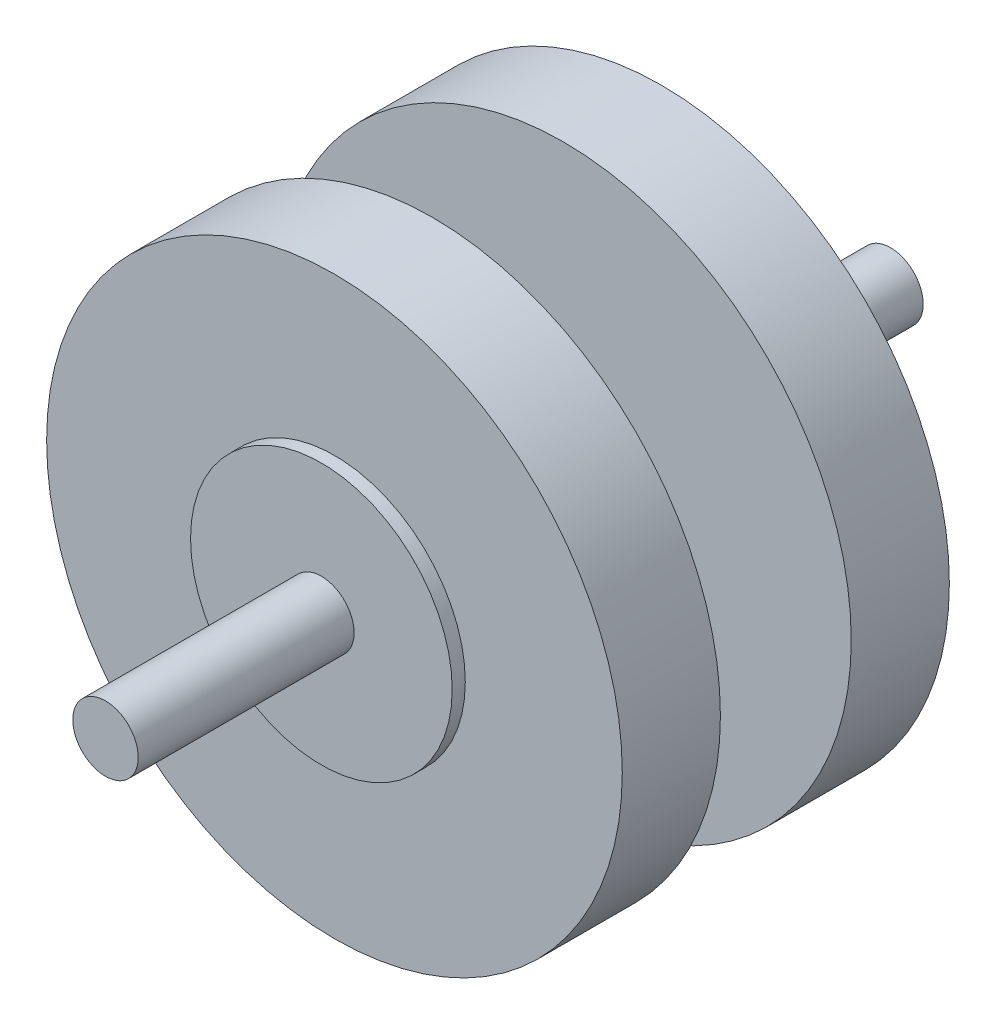
SolidWorks part; units mm, degrees
ref_plane "Płaszczyzna przednia" through (0, 0, 0) normal (0, 0, 1) x (1, 0, 0)
ref_plane "Płaszczyzna górna" through (0, 0, 0) normal (0, 1, 0) x (1, 0, 0)
ref_plane "Płaszczyzna prawa" through (0, 0, 0) normal (1, 0, 0) x (0, 0, -1)
sketch "Szkic1" plane through (0, 0, 0) normal (0, 0, 1) x (1, 0, 0)
  line L0 (0, 5) -> (0, -5) construction
  arc A0 (0, -5) -> (0, 5) centre (0, 0) ccw construction
  circle A1 centre (0, 0) radius 5
extrude "Dodanie-wyciągnięcie1" add sketch "Szkic1" against normal blind 33
sketch "Szkic2" plane through (0, 0, -33) normal (0, 0, -1) x (-1, 0, 0)
  circle A0 centre (0, 0) radius 20
  dimension "D1" = 40
extrude "Dodanie-wyciągnięcie2" add sketch "Szkic2" along normal blind 2
sketch "Szkic3" plane through (0, 0, -35) normal (0, 0, -1) x (-1, 0, 0)
  circle A0 centre (0, 0) radius 44
  dimension "D1" = 88
extrude "Dodanie-wyciągnięcie3" add sketch "Szkic3" along normal blind 15
sketch "Szkic5" plane through (0, 0, -50) normal (0, 0, -1) x (-1, 0, 0)
  circle A0 centre (9.135, -17.7919) radius 5 construction
  circle A1 centre (9.135, -17.7919) radius 5
extrude "Dodanie-wyciągnięcie6" add sketch "Szkic5" along normal blind 20
sketch "Szkic6" plane through (0, 0, -70) normal (0, 0, -1) x (-1, 0, 0)
  circle A0 centre (0, 0) radius 44 construction
  circle A1 centre (0, 0) radius 44
extrude "Dodanie-wyciągnięcie7" add sketch "Szkic6" along normal blind 15
sketch "Szkic7" plane through (0, 0, -85) normal (0, 0, -1) x (-1, 0, 0)
  circle A0 centre (0, 0) radius 20 construction
  circle A1 centre (0, 0) radius 20
extrude "Dodanie-wyciągnięcie8" add sketch "Szkic7" along normal blind 2
sketch "Szkic8" plane through (0, 0, -87) normal (0, 0, -1) x (-1, 0, 0)
  circle A0 centre (0, 0) radius 5 construction
  circle A1 centre (0, 0) radius 5
extrude "Dodanie-wyciągnięcie9" add sketch "Szkic8" along normal blind 33
